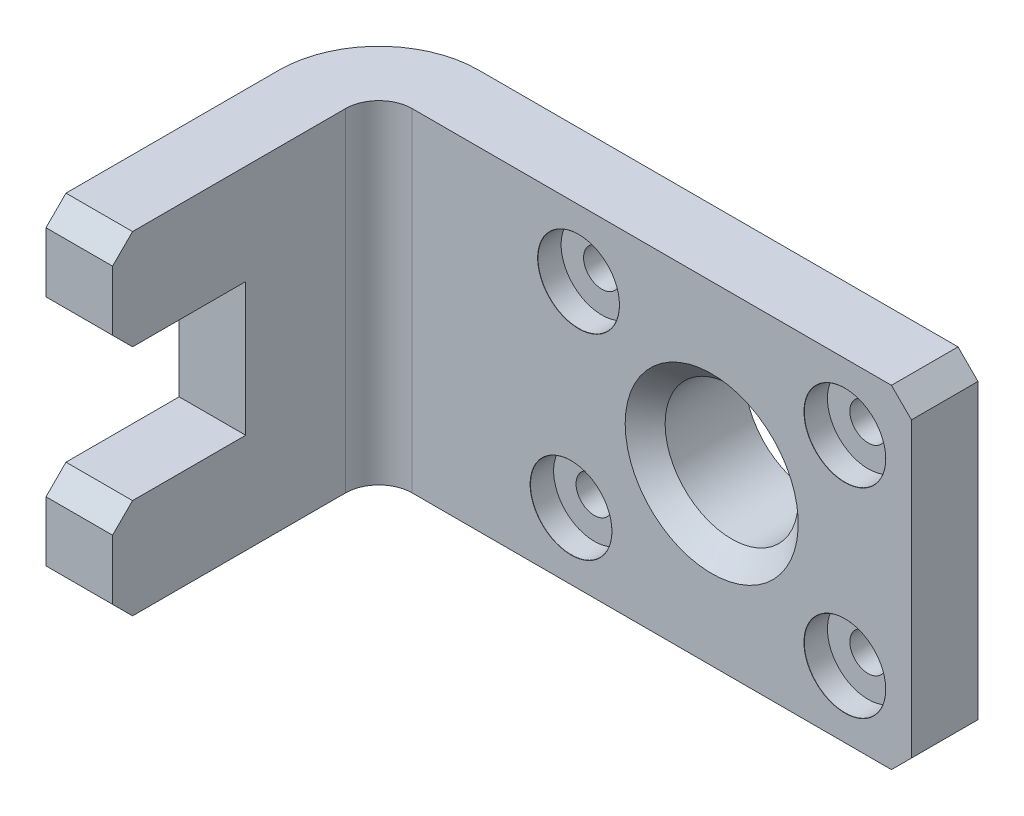
SolidWorks part; units mm, degrees
ref_plane "Front Plane" through (0, 0, 0) normal (0, 0, 1) x (1, 0, 0)
ref_plane "Top Plane" through (0, 0, 0) normal (0, 1, 0) x (1, 0, 0)
ref_plane "Right Plane" through (0, 0, 0) normal (1, 0, 0) x (0, 0, -1)
sketch "Sketch1" plane through (0, 0, 0) normal (0, 0, 1) x (1, 0, 0)
  line L5 (0, 0) -> (80, 0)
  line L6 (0, 0) -> (0, 50)
  line L7 (0, 50) -> (80, 50)
  line L8 (80, 0) -> (80, 50)
  dimension "D1" = 50
  dimension "D2" = 80
extrude "Boss-Extrude1" add sketch "Sketch1" along normal blind 10
sketch "Sketch2" plane through (0, 0, 0) normal (-1, 0, 0) x (0, 0, 1)
  line L13 (0, 0) -> (50, 0)
  line L14 (0, 0) -> (0, 50)
  line L15 (0, 50) -> (50, 50)
  line L16 (50, 0) -> (50, 50)
  dimension "D1" = 50
  dimension "D2" = 50
extrude "Boss-Extrude2" add sketch "Sketch2" along normal blind 10
sketch "Sketch5" plane through (0, 0, 50) normal (0, 0, 1) x (1, 0, 0)
  line L0 (-10, 0) -> (-10, 50) construction
  line L1 (-10, 35) -> (0, 35)
  line L2 (-10, 35) -> (-10, 15)
  line L3 (-10, 15) -> (0, 15)
  line L4 (0, 35) -> (0, 15)
  line L5 (0, 0) -> (0, 50) construction
  line L6 (-10, 50) -> (0, 50) construction
  line L7 (-10, 0) -> (0, 0) construction
  point P10 (-5, 15)
  dimension "D1" = 20
  dimension "D2" = 15
  dimension "D3" = 15
extrude "Cut-Extrude2" cut sketch "Sketch5" against normal blind 20 contours L1 L4 L3 L2
sketch "Sketch10" plane through (0, 0, 0) normal (0, 0, -1) x (-1, 0, 0)
  line L0 (-80, 50) -> (10, 50) construction
  line L2 (-80, 0) -> (-80, 50) construction
  circle A0 centre (-50, 25) radius 15
  dimension "D1" = 30
  dimension "D2" = 25
  dimension "D3" = 30
extrude "Boss-Extrude3" add sketch "Sketch10" along normal blind 5
sketch "Sketch13" plane through (0, 0, -5) normal (0, 0, -1) x (-1, 0, 0)
  line L0 (-80, 50) -> (10, 50) construction
  line L1 (-80, 0) -> (-80, 50) construction
  circle A0 centre (-50, 25) radius 10
  dimension "D1" = 20
  dimension "D2" = 25
  dimension "D3" = 30
extrude "Cut-Extrude4" cut sketch "Sketch13" against normal blind 15
chamfer "Chamfer1" distance 3 angle 45 1 edges at (40, 25, 10)
hole_wizard "CBORE for M5 Hex Head Bolt2" positions "Sketch18" profile "Sketch19" counterbore size "M5" standard "ISO" end condition through all
sketch "Sketch18" plane through (0, 0, 10) normal (0, 0, 1) x (1, 0, 0)
  line L0 (80, 50) -> (0, 50) construction
  line L1 (0, 0) -> (80, 0) construction
  line L4 (80, 0) -> (80, 50) construction
  point P0 (70, 40)
  point P2 (70, 10)
  point P4 (28.8696, 10)
  point P6 (30, 40)
  dimension "D1" = 40
  dimension "D2" = 10
  dimension "D3" = 40
  dimension "D4" = 10
  dimension "D5" = 10
  dimension "D6" = 10
  dimension "D7" = 10
sketch "Sketch19" plane through (70, 40, 10) normal (1, 0, 0) x (0, -1, 0)
  line L0 (0, 0) -> (0, 15)
  line L1 (0, 15) -> (2.75, 15)
  line L3 (2.75, 15) -> (2.75, 3.5)
  line L4 (6.119, 3.5) -> (2.75, 3.5)
  line L5 (6.119, 3.5) -> (6.119, 0.021)
  line L6 (6.119, 0.021) -> (6.144, 0)
  line L7 (6.144, 0) -> (0, 0)
  line L8 (-6.119, 0.021) -> (-6.144, 0) construction
  line L11 (0, -6.35) -> (0, 107.95) construction
  dimension "Thru Hole Dia." = 5.5
  dimension "Thru Hole Depth" = 15
  dimension "C'Bore Dia." = 12.238
  dimension "C'Bore Depth" = 3.5
  dimension "Near C'Sink Dia." = 12.288
  dimension "Near C'Sink Angle" = 100
chamfer "Chamfer2" distance 3 angle 45 1 edges at (-5, 50, 50)
chamfer "Chamfer3" distance 3 angle 45 1 edges at (-5, 35, 50)
chamfer "Chamfer4" distance 3 angle 45 4 edges at (80, 50, 5) (80, 0, 5) (-5, 0, 50) (-5, 15, 50)
fillet "Fillet1" radius 5 1 edges at (0, 25, 10)
fillet "Fillet2" radius 15 1 edges at (-10, 25, 0)
